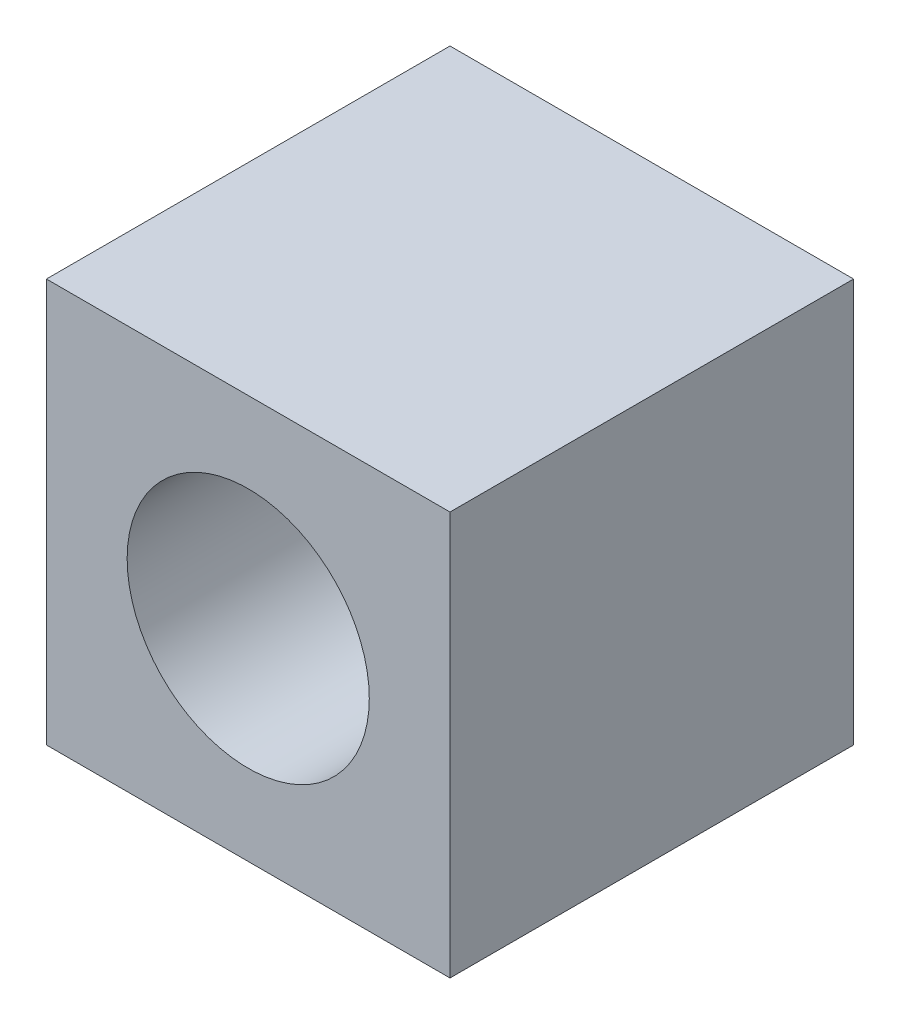
SolidWorks part; units mm, degrees
ref_plane "Front Plane" through (0, 0, 0) normal (0, 0, 1) x (1, 0, 0)
ref_plane "Top Plane" through (0, 0, 0) normal (0, 1, 0) x (1, 0, 0)
ref_plane "Right Plane" through (0, 0, 0) normal (1, 0, 0) x (0, 0, -1)
sketch "Sketch1" plane through (0, 0, 0) normal (0, 1, 0) x (1, 0, 0)
  line L0 (0, 0) -> (0, 10)
  line L1 (0, 0) -> (10, 0)
  line L2 (0, 10) -> (10, 10)
  line L3 (10, 10) -> (10, 0)
extrude "Boss-Extrude1" add sketch "Sketch1" along normal blind 10
sketch "Sketch2" plane through (0, 0, 0) normal (0, 0, 1) x (1, 0, 0)
  line L0 (0, 10) -> (10, 0) construction
  circle A0 centre (5, 5) radius 3
extrude "Cut-Extrude1" cut sketch "Sketch2" against normal blind 10
